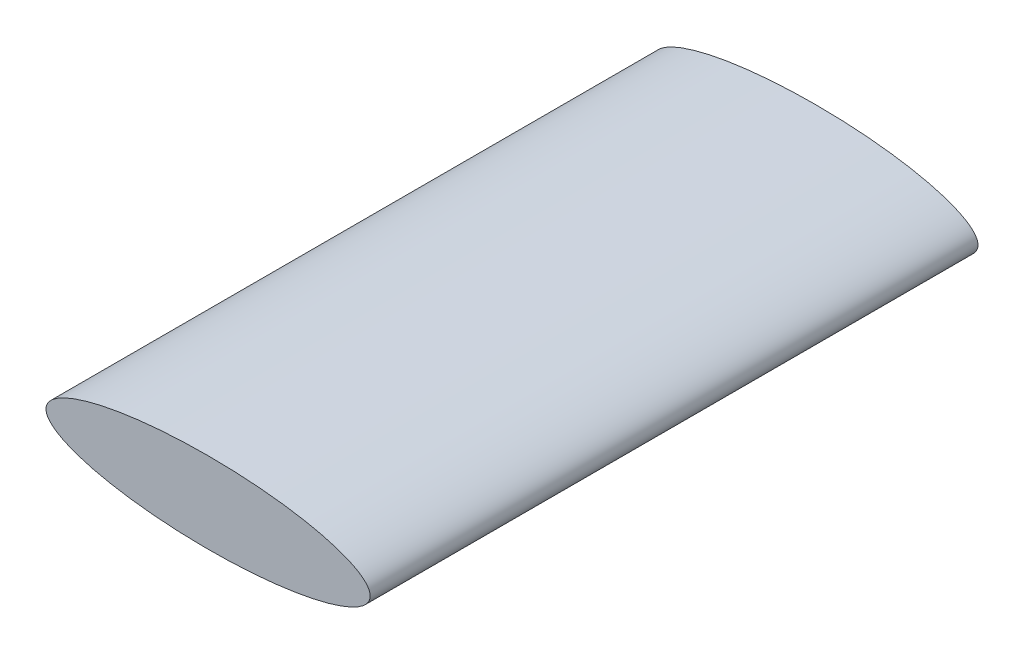
SolidWorks part; units mm, degrees
ref_plane "Plane1" through (0, 0, 0) normal (0, 0, 1) x (1, 0, 0)
ref_plane "Plane2" through (0, 0, 0) normal (0, 1, 0) x (1, 0, 0)
ref_plane "Plane3" through (0, 0, 0) normal (1, 0, 0) x (0, 0, -1)
sketch "Эскиз1" plane through (0, 0, 0) normal (0, 0, 1) x (1, 0, 0)
  ellipse E0 centre (1000, 400) end of major axis (200, 400) minor radius 200
extrude "Вытянуть1" add sketch "Эскиз1" against normal blind 3000
